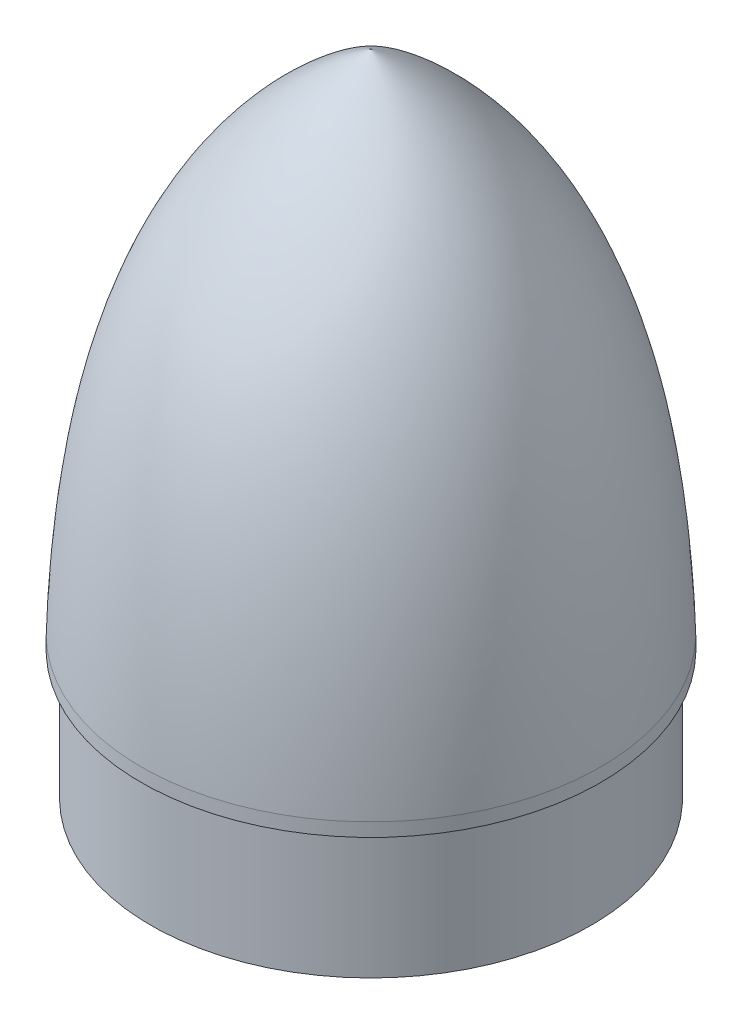
SolidWorks part; units mm, degrees
ref_plane "Front Plane" through (0, 0, 0) normal (0, 0, 1) x (1, 0, 0)
ref_plane "Top Plane" through (0, 0, 0) normal (0, 1, 0) x (1, 0, 0)
ref_plane "Right Plane" through (0, 0, 0) normal (1, 0, 0) x (0, 0, -1)
sketch "Sketch1" plane through (0, 0, 0) normal (0, 0, 1) x (1, 0, 0)
  line L0 (-13.3324, 13.1774) -> (-13.3324, -5.8226)
  line L1 (-13.3324, 13.1774) -> (-14.7324, 13.1774)
  line L2 (-14.7324, 13.1774) -> (-14.7324, 15.1774)
  line L8 (-10.3443, 32.853) -> (-6.8742, 48.8155)
  line L9 (-6.8742, 48.8155) -> (-2.016, 63.5635)
  line L10 (-2.016, 63.5635) -> (10.9912, 79.7255)
  line L11 (10.9912, 79.7255) -> (19.2676, 86.9882)
  line L12 (19.2676, 86.9882) -> (19.2676, 90.1774)
  line L16 (-13.3324, -5.8226) -> (-12.3324, -5.8226)
  line L17 (-12.3324, -5.8226) -> (-12.3324, 15.1774)
  line L18 (-12.3324, 15.1774) -> (-10.3443, 32.853)
  spline S0 degree 3 poles (19.2676, 90.1774) (-8.3107, 74.8433) (-13.7616, 43.1643) (-14.7324, 15.1774) knots 0 0 0 0 1 1 1 1
  dimension "D1" = 19
  dimension "D2" = 2
  dimension "D3" = 34
  dimension "D4" = 77
  dimension "D5" = 1
  dimension "D6" = 32.6
revolve "Revolve1" add sketch "Sketch1" angle 360 about L12
